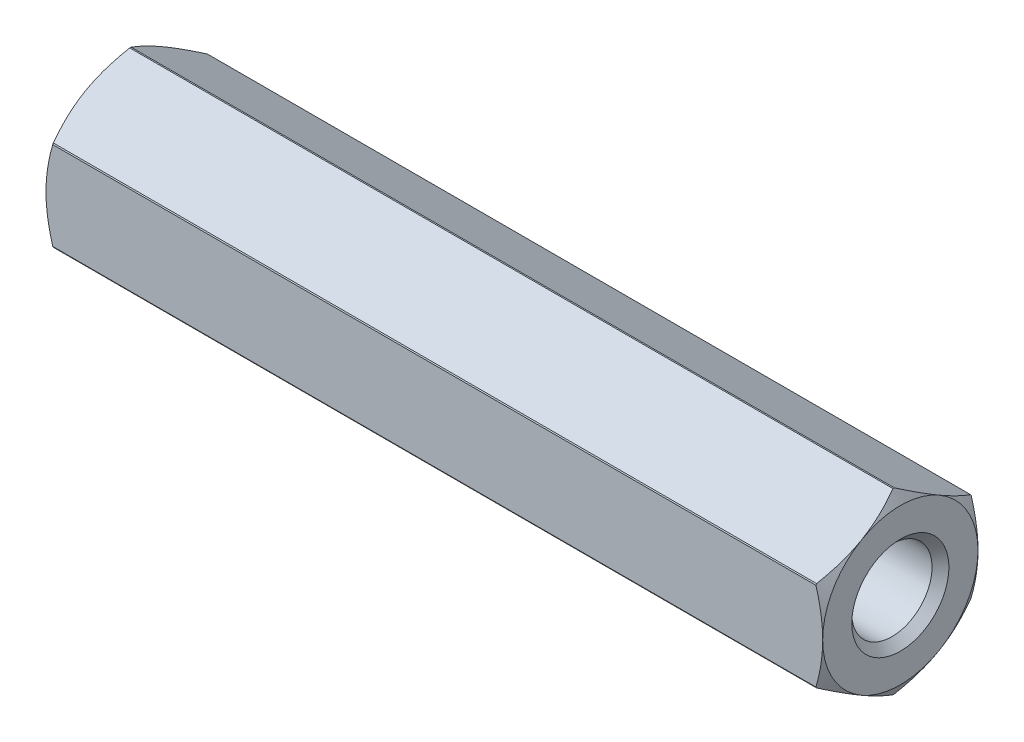
SolidWorks part; units mm, degrees
ref_plane "Front" through (0, 0, 0) normal (0, 0, 1) x (1, 0, 0)
ref_plane "Top" through (0, 0, 0) normal (0, 1, 0) x (1, 0, 0)
ref_plane "Right" through (0, 0, 0) normal (1, 0, 0) x (0, 0, -1)
ref_plane "Plane1" through (0, 0, 0) normal (0, 0, 1) x (1, 0, 0)
sketch "Sketch1" plane through (0, 0, 0) normal (0, 0, 1) x (1, 0, 0)
  line L0 (0, 0) -> (0, 4)
  line L1 (0, 4) -> (0.3464, 4.6)
  line L2 (0.3464, 4.6) -> (39.6536, 4.6)
  line L3 (39.6536, 4.6) -> (40, 4)
  line L4 (40, 4) -> (40, 0)
  line L5 (40, 0) -> (0, 0)
  line L6 (40, 0) -> (0, 0) construction
revolve "Revolve1" add sketch "Sketch1" angle 360 about L6
ref_plane "Plane2" through (0, 0, 0) normal (1, 0, 0) x (0, 0, -1)
sketch "Sketch2" plane through (0, 0, 0) normal (1, 0, 0) x (0, 0, -1)
  line L0 (-8, 8) -> (-8, -8)
  line L1 (-8, -8) -> (8, -8)
  line L2 (8, -8) -> (8, 8)
  line L3 (8, 8) -> (-8, 8)
  line L4 (-4, 2.3094) -> (-4, -2.3094)
  line L5 (-4, -2.3094) -> (0, -4.6188)
  line L6 (0, -4.6188) -> (4, -2.3094)
  line L7 (4, -2.3094) -> (4, 2.3094)
  line L8 (4, 2.3094) -> (0, 4.6188)
  line L9 (0, 4.6188) -> (-4, 2.3094)
extrude "Cut-Extrude1" cut sketch "Sketch2" along normal blind 40
ref_plane "Plane3" through (0, 0, 0) normal (0, 0, 1) x (1, 0, 0)
sketch "Sketch3" plane through (0, 0, 0) normal (0, 0, 1) x (1, 0, 0)
  line L0 (0, 0) -> (0, 2.5)
  line L1 (0, 2.5) -> (0.433, 2.067)
  line L2 (0.433, 2.067) -> (11.3066, 2.067)
  line L3 (11.3066, 2.067) -> (12.5, 0)
  line L4 (12.5, 0) -> (0, 0)
  line L5 (12.5, 0) -> (0, 0) construction
revolve "Cut-Revolve1" cut sketch "Sketch3" angle 360 about L5
cosmetic thread "Cosmetic Thread1" parameters "D1"=9.567, "D2"=5
ref_plane "Plane4" through (0, 0, 0) normal (0, 0, 1) x (1, 0, 0)
sketch "Sketch4" plane through (0, 0, 0) normal (0, 0, 1) x (1, 0, 0)
  line L0 (27.5, 0) -> (28.6934, 2.067)
  line L1 (28.6934, 2.067) -> (39.567, 2.067)
  line L2 (39.567, 2.067) -> (40, 2.5)
  line L3 (40, 2.5) -> (40, 0)
  line L4 (40, 0) -> (27.5, 0)
  line L5 (40, 0) -> (27.5, 0) construction
revolve "Cut-Revolve2" cut sketch "Sketch4" angle 360 about L5
cosmetic thread "Cosmetic Thread2" parameters "D1"=9.567, "D2"=5
